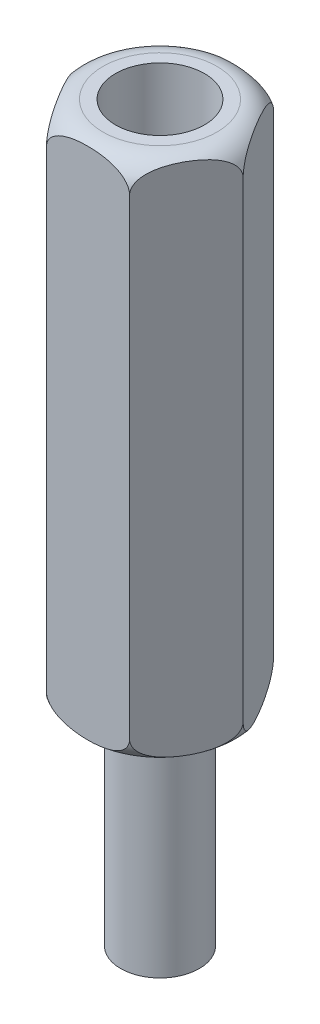
SolidWorks part; units mm, degrees
material "Brass"
ref_plane "Front Plane" through (0, 0, 0) normal (0, 0, 1) x (1, 0, 0)
ref_plane "Top Plane" through (0, 0, 0) normal (0, 1, 0) x (1, 0, 0)
ref_plane "Right Plane" through (0, 0, 0) normal (1, 0, 0) x (0, 0, -1)
sketch "Sketch1" plane through (0, 0, 0) normal (0, 1, 0) x (1, 0, 0)
  line L1 (3.1754, 0) -> (1.5877, 2.75)
  line L2 (1.5877, 2.75) -> (-1.5877, 2.75)
  line L3 (-1.5877, 2.75) -> (-3.1754, 0)
  line L4 (-3.1754, 0) -> (-1.5877, -2.75)
  line L5 (-1.5877, -2.75) -> (1.5877, -2.75)
  line L6 (1.5877, -2.75) -> (3.1754, 0)
  circle A0 centre (0, 0) radius 2.75 construction
  dimension "D1" = 5.5
extrude "Boss-Extrude1" add sketch "Sketch1" along normal blind 20
hole_wizard "M3 Clearance Hole1" positions "Sketch3" profile "Sketch2" hole size "M3" standard "ISO"
sketch "Sketch3" plane through (0, 20, 0) normal (0, 1, 0) x (-1, 0, 0)
  point P0 (0, 0)
sketch "Sketch2" plane through (0, 20, 0) normal (1, 0, 0) x (0, 0, 1)
  line L0 (0, 0) -> (0, 13.0215)
  line L1 (0, 13.0215) -> (1.7, 12)
  line L2 (1.7, 12) -> (1.7, 0)
  line L5 (1.7, 0) -> (0, 0)
  line L10 (0, 13.0215) -> (-1.7, 12) construction
  line L11 (0, -6.35) -> (0, 107.95) construction
  dimension "Hole Dia." = 3.4
  dimension "Hole Depth" = 12
  dimension "Drill Angle" = 118
sketch "Sketch4" plane through (0, 0, 0) normal (0, 0, 1) x (1, 0, 0)
  line L0 (-3.1754, 20) -> (-3.1754, 0) construction
  line L1 (-3.1754, 20) -> (-1.5877, 20) construction
  line L4 (-3.1754, 0) -> (-1.5877, 0) construction
  line L6 (-2.1754, 20) -> (-3.1754, 20)
  line L7 (-3.1754, 20) -> (-3.1754, 19)
  line L8 (-3.1754, 1) -> (-3.1754, 0)
  line L9 (-3.1754, 0) -> (-2.1754, 0)
  line L14 (0, 20) -> (0, 0) construction
  line L15 (-1.5877, 20) -> (1.5877, 20) construction
  arc A0 (-3.1754, 19) -> (-2.1754, 20) centre (-2.1754, 19) cw
  arc A2 (-3.1754, 1) -> (-2.1754, 0) centre (-2.1754, 1) ccw
  dimension "D1" = 1
revolve "Cut-Revolve1" cut sketch "Sketch4" angle 360 about L14
sketch "Sketch5" plane through (0, 0, 0) normal (0, -1, 0) x (1, 0, 0)
  circle A0 centre (0, 0) radius 1.5
  dimension "D1" = 3
extrude "Boss-Extrude2" add sketch "Sketch5" along normal blind 8
